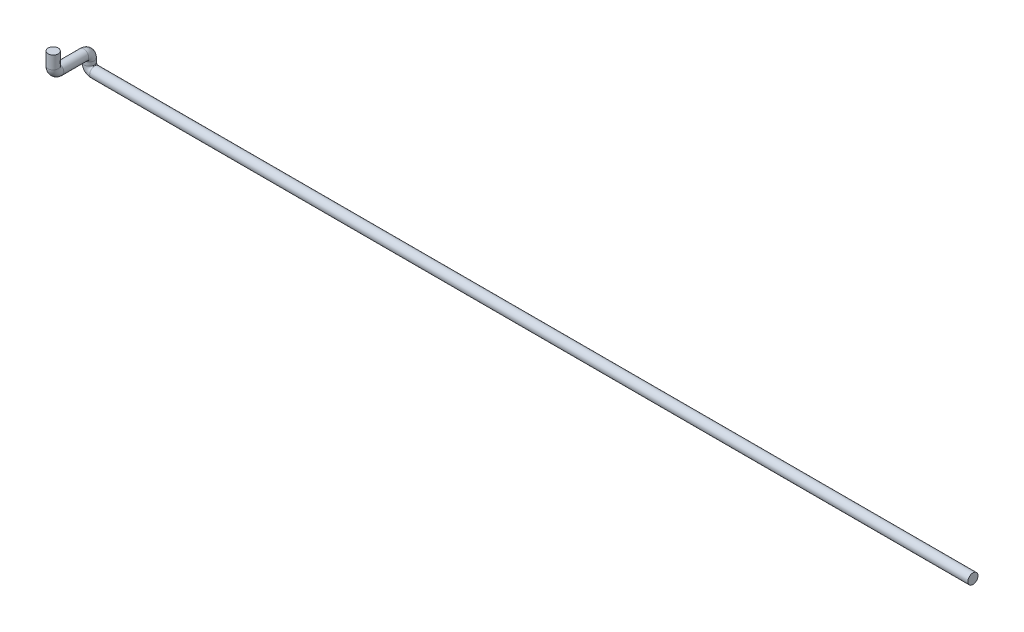
SolidWorks part; units mm, degrees
ref_plane "Alzado" through (0, 0, 0) normal (0, 0, 1) x (1, 0, 0)
ref_plane "Planta" through (0, 0, 0) normal (0, 1, 0) x (1, 0, 0)
ref_plane "Vista lateral" through (0, 0, 0) normal (1, 0, 0) x (0, 0, -1)
sketch3d "Croquis3D1"
  line L0 (0, 0, 0) -> (-2374, 0, 0)
  line L1 (-2389, 15, 0) -> (-2389, 25, 0)
  line L2 (-2389, 40, 15) -> (-2389, 40, 82.5)
  line L3 (-2389, 55, 97.5) -> (-2389, 90, 97.5)
  arc A0 (-2389, 25, 0) -> (-2389, 40, 15) centre (-2389, 25, 15) ccw
  arc A1 (-2374, 0, 0) -> (-2389, 15, 0) centre (-2374, 15, 0) ccw
  arc A2 (-2389, 40, 82.5) -> (-2389, 55, 97.5) centre (-2389, 55, 82.5) ccw
  point P8 (-2389, 40, 0)
  point P9 (-2374, 25, 15)
  point P12 (-2389, 0, 0)
  point P13 (-2374, 15, -15)
  point P16 (-2389, 40, 97.5)
  point P17 (-2404, 55, 82.5)
  dimension "D5" = 15
  dimension "D1" = 2389
  dimension "D2" = 40
  dimension "D3" = 97.5
  dimension "D4" = 50
sketch "Croquis1" plane through (0, 0, 0) normal (1, 0, 0) x (0, 0, -1)
  circle A0 centre (0, 0) radius 13.7
  dimension "D1" = 27.4
sweep "Barrer1" add profiles "Croquis1" path "Croquis3D1"
